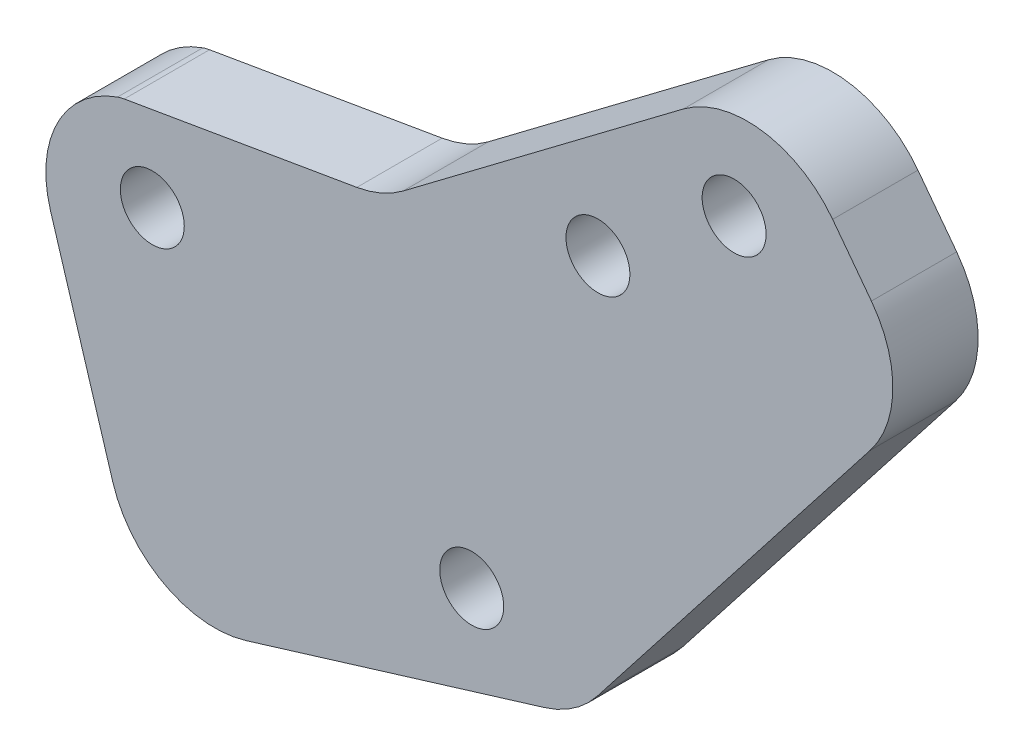
SolidWorks part; units mm, degrees
material "A-玻璃纤维"
ref_plane "前视基准面" through (0, 0, 0) normal (0, 0, 1) x (1, 0, 0)
ref_plane "上视基准面" through (0, 0, 0) normal (0, 1, 0) x (1, 0, 0)
ref_plane "右视基准面" through (0, 0, 0) normal (1, 0, 0) x (0, 0, -1)
sketch "草图1" plane through (0, 0, 0) normal (0, 0, 1) x (1, 0, 0)
  line L10 (12.6675, 18.143) -> (-5.445, 4.4943)
  line L11 (12.6675, 18.143) -> (29.4316, -4.1038)
  line L12 (-5.445, 4.4943) -> (-17.6947, 2.4021)
  line L13 (-11.8472, -16.724) -> (29.4316, -4.1038)
  line L14 (-21.0143, -3.8413) -> (-18.0906, -13.4044)
  circle A14 centre (11.054, 11.9759) radius 1.5
  circle A15 centre (4.6649, 7.1613) radius 1.5
  circle A16 centre (-16.2383, -1.3354) radius 1.5
  circle A17 centre (-1.2542, -9.3026) radius 1.5
  arc A18 (-17.6947, 2.4021) -> (-21.0143, -3.8413) centre (-16.2328, -2.3795) ccw
  arc A19 (-18.0906, -13.4044) -> (-11.8472, -16.724) centre (-13.3091, -11.9425) ccw
  point P17 (-5.445, 4.4943)
  dimension "D1" = 3
  dimension "D2" = 5
  dimension "D3" = 4.6649
  dimension "D4" = 11.054
  dimension "D5" = 12.6675
  dimension "D6" = 29.4316
  dimension "D7" = 1.2542
  dimension "D8" = 5.445
  dimension "D9" = 11.8472
  dimension "D10" = 13.3091
  dimension "D11" = 16.2328
  dimension "D12" = 16.2383
  dimension "D13" = 17.6947
  dimension "D14" = 2.4021
  dimension "D15" = 4.4943
  dimension "D16" = 7.1613
  dimension "D17" = 11.9759
  dimension "D19" = 1.3354
  dimension "D23" = 9.3026
extrude "凸台-拉伸1" add sketch "草图1" along normal blind 4
fillet "圆角2" radius 5 2 edges at (12.6675, 18.143, 2) (-5.445, 4.4943, 2)
sketch "草图2" plane through (0, 0, 0) normal (0, 0, -1) x (-1, 0, 0)
  line L0 (-19.8026, 8.6743) -> (-3.6643, -11.9817)
  line L1 (-29.4316, -4.1038) -> (-15.6765, 14.1498) construction
  line L2 (11.8472, -16.724) -> (-29.4316, -4.1038) construction
  line L8 (4.475, 5.2252) -> (-8.6743, 15.1339)
  line L9 (-15.6765, 14.1498) -> (-29.4316, -4.1038)
  line L10 (-29.4316, -4.1038) -> (11.8472, -16.724)
  line L11 (18.0906, -13.4044) -> (21.0143, -3.8413)
  line L12 (17.6947, 2.4021) -> (6.6423, 4.2898)
  line L14 (-19.8026, 8.6743) -> (-29.4316, -4.1038)
  line L15 (-29.4316, -4.1038) -> (-3.6643, -11.9817)
  arc A4 (-8.6743, 15.1339) -> (-15.6765, 14.1498) centre (-11.6834, 11.1407) ccw
  arc A5 (11.8472, -16.724) -> (18.0906, -13.4044) centre (13.3091, -11.9425) ccw
  arc A6 (21.0143, -3.8413) -> (17.6947, 2.4021) centre (16.2328, -2.3795) ccw
  arc A7 (4.475, 5.2252) -> (6.6423, 4.2898) centre (7.4841, 9.2184) ccw
  dimension "D2" = 35
  dimension "D3" = 16
  dimension "D1" = 0
extrude "切除-拉伸1" cut sketch "草图2" against normal through all
fillet "圆角3" radius 5 2 edges at (19.8026, 8.6743, 2) (3.6643, -11.9817, 2)
fillet "圆角4" radius 2 1 edges at (-17.6947, 2.4021, 2)
